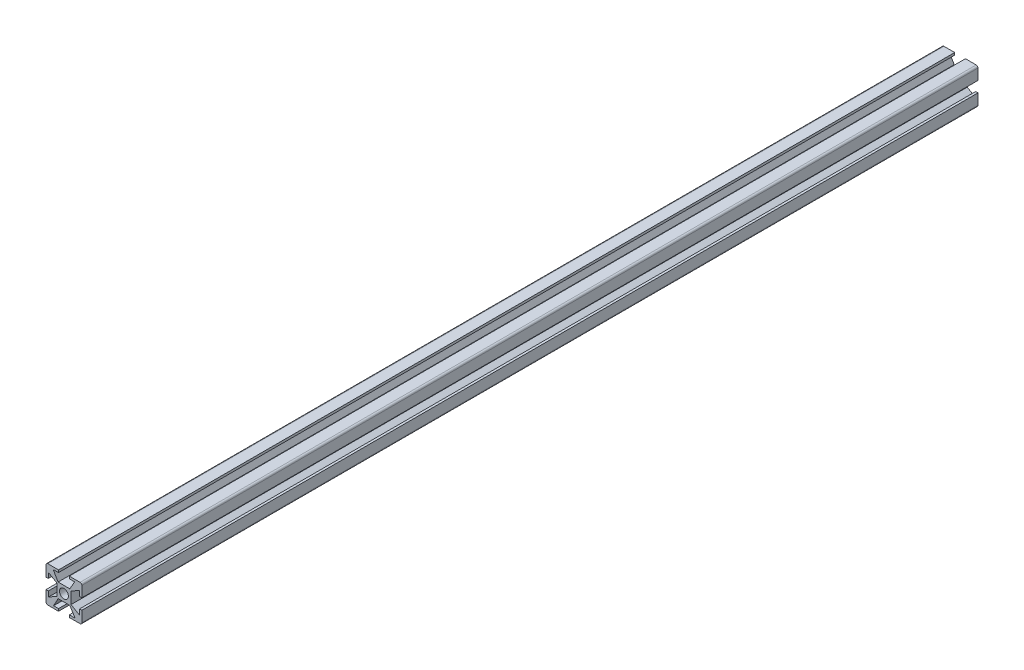
SolidWorks part; units mm, degrees
ref_plane "Alzado" through (0, 0, 0) normal (0, 0, 1) x (1, 0, 0)
ref_plane "Planta" through (0, 0, 0) normal (0, 1, 0) x (1, 0, 0)
ref_plane "Vista lateral" through (0, 0, 0) normal (1, 0, 0) x (0, 0, -1)
sketch "Croquis1" plane through (0, 0, 0) normal (0, 0, 1) x (1, 0, 0)
  line L0 (-3, 10) -> (3, 10)
  line L1 (-9, 10) -> (9, 10)
  line L2 (-10, 9) -> (-10, -9)
  line L3 (-9, -10) -> (9, -10)
  line L4 (10, 9) -> (10, -9)
  line L5 (-10, 10) -> (10, -10) construction
  line L6 (-10, -10) -> (10, 10) construction
  line L7 (-4, 4) -> (4, 4)
  line L8 (-4, 4) -> (-4, -4)
  line L9 (-4, -4) -> (4, -4)
  line L10 (4, 4) -> (4, -4)
  line L11 (-4, 4) -> (4, -4) construction
  line L12 (-4, -4) -> (4, 4) construction
  line L13 (3, 10) -> (3, 8.7)
  line L14 (-3.25, 4) -> (3.25, 4)
  line L15 (0, 10) -> (0, -10) construction
  line L16 (-10, 0) -> (10, 0) construction
  line L20 (-3, 10) -> (-3, 8.7)
  line L22 (3, -10) -> (3, -8.7)
  line L23 (-3, -10) -> (3, -10)
  line L24 (-3, -10) -> (-3, -8.7)
  line L25 (-5.75, -8.7) -> (-3, -8.7)
  line L26 (-5.75, -8.7) -> (-3.25, -4)
  line L27 (-3.25, -4) -> (3.25, -4)
  line L28 (6.25, -8.7) -> (3.25, -4)
  line L29 (3, -8.7) -> (6.25, -8.7)
  line L30 (-10, 3) -> (-10, -3)
  line L31 (-4, 3.25) -> (-4, -3.25)
  line L32 (-10, 3) -> (-8.7, 3)
  line L33 (-8.7, -6) -> (-8.7, -3)
  line L34 (-8.7, 6) -> (-4, 3.25)
  line L35 (-8.7, -6) -> (-4, -3.25)
  line L36 (-10, -3) -> (-8.7, -3)
  line L37 (-8.7, 3) -> (-8.7, 6)
  line L38 (8.7, -6) -> (4, -3.25)
  line L39 (4, 3.25) -> (4, -3.25)
  line L40 (8.7, 6) -> (4, 3.25)
  line L41 (8.7, 3) -> (8.7, 6)
  line L42 (10, 3) -> (8.7, 3)
  line L43 (10, 3) -> (10, -3)
  line L44 (10, -3) -> (8.7, -3)
  line L45 (8.7, -6) -> (8.7, -3)
  line L46 (-6, 8.7) -> (-3, 8.7)
  line L47 (-6, 8.7) -> (-3.25, 4)
  line L48 (6, 8.7) -> (3.25, 4)
  line L49 (3, 8.7) -> (6, 8.7)
  circle A0 centre (0, 0) radius 2.5
  arc A1 (-10, -9) -> (-9, -10) centre (-9, -9) ccw
  arc A2 (9, -10) -> (10, -9) centre (9, -9) ccw
  arc A3 (9, 10) -> (10, 9) centre (9, 9) cw
  arc A4 (-9, 10) -> (-10, 9) centre (-9, 9) ccw
  point P0 (0, 0)
  point P6 (0, 0)
  point P14 (0, 10)
  point P18 (0, 4)
  point P25 (0, 8.7)
  point P37 (-10, 0)
  point P40 (-4, 0)
  point P44 (-8.7, 0)
  point P56 (0, 8.7)
  dimension "D12" = 5
  dimension "D13" = 1
  dimension "D1" = 20
  dimension "D2" = 20
  dimension "D3" = 8
  dimension "D4" = 8
  dimension "D5" = 6
  dimension "D6" = 6.5
  dimension "D7" = 12
  dimension "D8" = 6.5
  dimension "D9" = 6
  dimension "D10" = 1.3
  dimension "D11" = 12
extrude "Saliente-Extruir4" add sketch "Croquis1" along normal blind 500 contours L1 A4 L2 L32 L37 L34 L8 L7 L47 L46 L20 | A3 L1 L13 L49 L48 L7 L10 L40 L41 L42 L4 | L3 A2 L4 L44 L45 L38 L10 L9 L28 L29 L22 | L2 A1 L3 L24 L25 L26 L9 L8 L35 L33 L36 | L10 L7 L8 L9 A0
